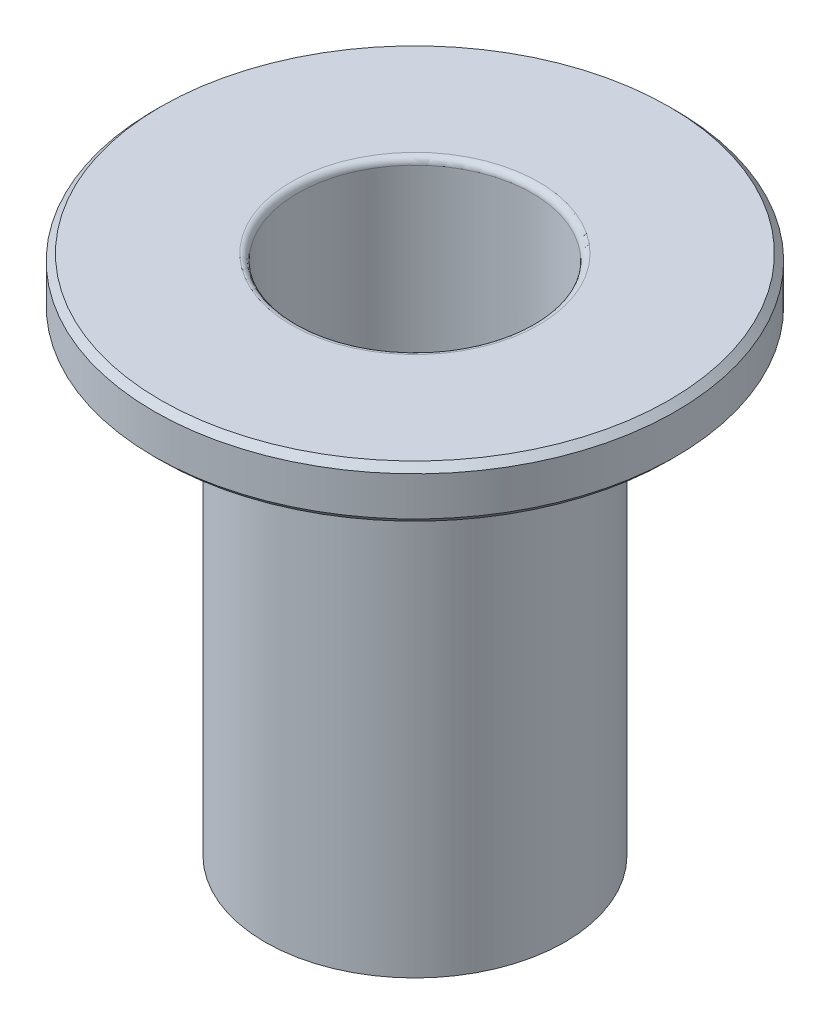
SolidWorks part; units mm, degrees
material "合金鋼"
ref_plane "正面" through (0, 0, 0) normal (0, 0, 1) x (1, 0, 0)
ref_plane "平面" through (0, 0, 0) normal (0, 1, 0) x (1, 0, 0)
ref_plane "右側面" through (0, 0, 0) normal (1, 0, 0) x (0, 0, -1)
sketch "ｽｹｯﾁ1" plane through (0, 0, 0) normal (0, 1, 0) x (1, 0, 0)
  circle A0 centre (0, 0) radius 10
extrude "ﾎﾞｽ - 押し出し1" add sketch "ｽｹｯﾁ1" along normal blind 2
sketch "ｽｹｯﾁ2" plane through (0, 0, 0) normal (0, -1, 0) x (1, 0, 0)
  circle A0 centre (0, 0) radius 5.75
extrude "ﾎﾞｽ - 押し出し2" add sketch "ｽｹｯﾁ2" along normal blind 18
sketch "ｽｹｯﾁ3" plane through (0, 2, 0) normal (0, 1, 0) x (1, 0, 0)
  circle A0 centre (0, 0) radius 4.5
extrude "ｶｯﾄ - 押し出し1" cut sketch "ｽｹｯﾁ3" against normal up to next
chamfer "面取り1" distance 0.25 angle 45 2 edges at (0, 0, 10) (0, 2, 10)
fillet "ﾌｨﾚｯﾄ1" radius 0.25 2 edges at (0, -18, -4.5) (0, 2, 4.5)
